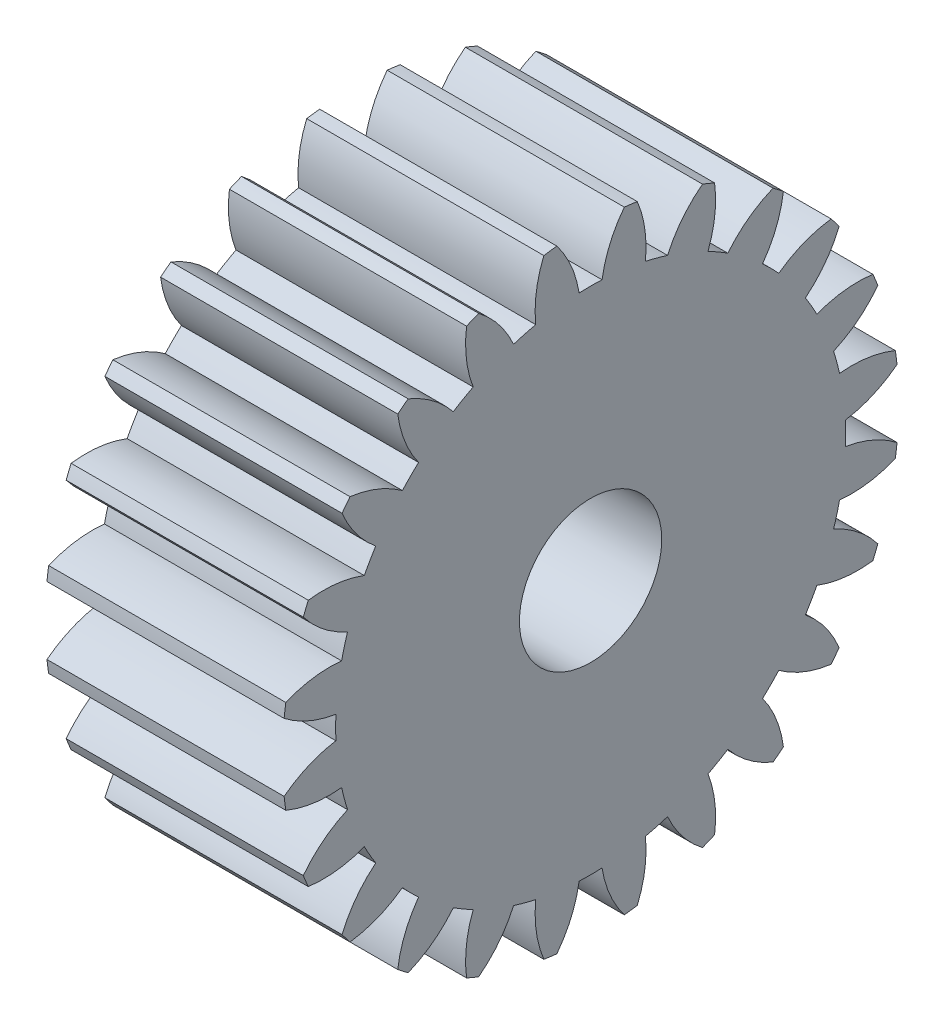
SolidWorks part; units mm, degrees
ref_plane "Plane1" through (0, 0, 0) normal (0, 0, 1) x (1, 0, 0)
ref_plane "Plane2" through (0, 0, 0) normal (0, 1, 0) x (1, 0, 0)
ref_plane "Plane3" through (0, 0, 0) normal (1, 0, 0) x (0, 0, -1)
other "Configuration Table"
sketch "HoldingSke" plane through (0, 0, 0) normal (0, 1, 0) x (1, 0, 0)
  line L0 (0, 0) -> (0.9135, -0.4067)
  line L1 (-15, 0) -> (100, 0) construction
  line L2 (0, 0) -> (-2.1039, 2.3779)
  line L3 (0, 0) -> (-11.863, 4.5341)
  line L4 (0, 0) -> (7.8894, 3.5126)
  line L5 (0, 0) -> (-46.8476, -17.4728)
  line L6 (0, 0) -> (-8.2896, -5.593)
  line L7 (-2.1039, 2.3779) -> (8.6586, 51.2059)
  line L8 (-76.2, 54.61) -> (-75.3, 54.61)
  line L9 (-71.009, 38.7566) -> (-53.1078, 45.2721)
  line L10 (-76.2, 71.12) -> (104.1128, 71.12)
  line L11 (0, 0) -> (-10, 0)
  line L12 (-76.2, 101.6) -> (-76.162, 101.6)
  line L13 (24.9733, 27.94) -> (52.9518, 28.4284)
  line L14 (24.9733, 27.94) -> (24.9743, 27.94)
  line L15 (24.9733, 27.94) -> (100.4006, 29.5858)
  line L16 (-63.627, -1) -> (-12.827, -1)
  circle A0 centre (0, 0) radius 2.5
  circle A1 centre (0, 0) radius 10.749
  circle A2 centre (0, 0) radius 37.5
  circle A3 centre (0, 0) radius 2.5
  dimension "MHD" = 21.498
  dimension "Hub_dia" = 75
  dimension "Bore" = 5
  dimension "MBD" = 5
  dimension "Num_teeth" = 24
  dimension "Pitch" = 1
  dimension "Overall_len" = 50
  dimension "Show_teeth" = 24
  dimension "Thickness" = 10
  dimension "OAL" = 50.0001
  dimension "T_dim" = 0.9
  dimension "Ap" = 20
  dimension "H" = 19.05
  dimension "Pitch_radius" = 180.3128
  dimension "Width" = 10
  dimension "Backlash" = 0.038
  dimension "Addendum_fac" = 1
  dimension "Dedendum_fac" = 1.25
  dimension "Clearance_fac" = 0.25
  dimension "Dedendum_add" = 0.001
  dimension "Module" = 1
sketch "BasProSke" plane through (0, 0, 0) normal (0, 1, 0) x (1, 0, 0)
  line L0 (-10, 0) -> (60, 0) construction
  line L1 (0, 0) -> (0, 13)
  line L2 (0, 0) -> (10, 0)
  line L3 (10, 0) -> (10, 13)
  line L4 (10, 13) -> (0, 13)
  dimension "Thickness" = 10
  dimension "Diameter" = 26
revolve "Base-Revolve" add sketch "BasProSke" angle 360 about L0
sketch "TooCutSke" plane through (0, 0, 0) normal (1, 0, 0) x (0, 0, -1)
  line L1 (0, 0) -> (0, 107) construction
  line L2 (0, 0) -> (-0.8513, 11.9698) construction
  line L3 (0, 0) -> (-3.127, 23.752) construction
  line L4 (-0.8513, 11.9698) -> (-1.5635, 11.876) construction
  arc A0 (0.4834, 10.7381) -> (-0.4834, 10.7381) centre (0, 0) ccw
  arc A1 (1.4409, 12.9455) -> (-1.4409, 12.9455) centre (0, 0) ccw
  circle A2 centre (0, 0) radius 12 construction
  circle A3 centre (0, 0) radius 11.2763 construction
  arc A4 (-0.4834, 10.7381) -> (-1.4409, 12.9455) centre (-5.2252, 9.9926) ccw
  arc A5 (1.4409, 12.9455) -> (0.4834, 10.7381) centre (5.2252, 9.9926) ccw
  dimension "Root_dia" = 21.498
  dimension "Overcut_dia" = 26.0508
  dimension "Pitch_dia" = 24
  dimension "Base_dia" = 22.5526
  dimension "Flank_rad" = 4.8
  dimension "Half_ang" = 7.5
  dimension "Half_CT" = 0.7183
extrude "ToothCut" cut sketch "TooCutSke" along normal through all
fillet "Breaks" [suppressed] radius 0.02
fillet "RootFillets" [suppressed] radius 0.251
pattern_circular "TeethCuts" count 24 every 15 about axis through (-10, 0, 0) along (1, 0, 0) of "ToothCut", "RootFillets", "Breaks"
sketch "HubNeaOneSke" plane through (0, 0, 0) normal (-1, 0, 0) x (0, 0, 1)
  circle A0 centre (0, 0) radius 10.749
  dimension "Diameter" = 21.498
extrude "HubNearOne" [suppressed] add sketch "HubNeaOneSke" along normal blind 40.0001
sketch "HubNeaBotSke" plane through (0, 0, 0) normal (-1, 0, 0) x (0, 0, 1)
  circle A0 centre (0, 0) radius 10.749
  dimension "Diameter" = 21.498
extrude "HubNearBoth" [suppressed] add sketch "HubNeaBotSke" along normal blind 20
ref_plane "FarPln" through (10, 0, 0) normal (1, 0, 0) x (0, 0, -1)
sketch "HubFarSke" plane through (10, 0, 0) normal (1, 0, 0) x (0, 0, -1)
  circle A0 centre (0, 0) radius 10.749
  dimension "Diameter" = 21.498
extrude "HubFar" [suppressed] add sketch "HubFarSke" along normal blind 20
sketch "BorSke" plane through (0, 0, 0) normal (1, 0, 0) x (0, 0, -1)
  circle A0 centre (0, 0) radius 2.5
  dimension "Diameter" = 5
extrude "Bore" cut sketch "BorSke" along normal mid plane 100.0001
sketch "KeySke" plane through (0, 0, 0) normal (1, 0, 0) x (0, 0, -1)
  line L0 (-1, 0) -> (-1, 3.4)
  line L1 (-1, 3.4) -> (1, 3.4)
  line L2 (1, 3.4) -> (1, 0)
  line L3 (0, 0) -> (0, 34) construction
  line L4 (-1, 0) -> (1, 0)
  dimension "Offset" = 3.4
  dimension "Width" = 2
extrude "Keyway" [suppressed] cut sketch "KeySke" along normal mid plane 100.0001
pattern_circular "Keyway2" [suppressed] count 2 every 90 about axis through (-10, 0, 0) along (1, 0, 0)
sketch "Sketch1" plane through (10, 0, 0) normal (1, 0, 0) x (0, 0, -1)
  circle A0 centre (0, 0) radius 3
  dimension "D1" = 6
extrude "Cut-Extrude1" cut sketch "Sketch1" against normal through all
equation "' \"Module@HoldingSke\" = 6.35"
equation "' \"Num_teeth@HoldingSke\" = 12"
equation "' \"Ap@HoldingSke\" =  20"
equation "' \"Ap@HoldingSke\" = 20"
equation "' \"Width@HoldingSke\" = 0.5 * 25.4"
equation "' \"Hub_dia@HoldingSke\"= 1 * 25.4"
equation "' \"Hub_dia@HoldingSke\" = 1 * 25.4"
equation "' \"Overall_len@HoldingSke\" = 1.0 * 25.4"
equation "' \"Bore@HoldingSke\" = 0.75 * 25.4"
equation "' \"T_dim@HoldingSke\" = 0.1 * 25.4"
equation "' \"Width@KeySke\" = 0.25 * 25.4"
equation "' \"Show_teeth@HoldingSke\" = 13"
equation "' \"Backlash@HoldingSke\" = 0.009 * 25.4"
equation "' \"Addendum_fac@HoldingSke\" = 1.0"
equation "' \"Dedendum_fac@HoldingSke\" = 1.25"
equation "' \"Dedendum_add@HoldingSke\" = 0.00005 * 25.4"
equation "' \"Clearance_fac@HoldingSke\" = 0.25"
equation "\"Pitch@HoldingSke\" = 1 / \"Module@HoldingSke\""
equation "\"Overcut_dia@TooCutSke\" = (\"Num_teeth@HoldingSke\" + 2 * \"Addendum_fac@HoldingSke\") / \"Pitch@HoldingSke\" + 0.002 * 25.4"
equation "\"Pitch_dia@TooCutSke\" = \"Num_teeth@HoldingSke\" / \"Pitch@HoldingSke\""
equation "\"Base_dia@TooCutSke\" = \"Num_teeth@HoldingSke\" / \"Pitch@HoldingSke\" * cos((\"Ap@HoldingSke\"  * 3.14159265 / 180))"
equation "\"Root_dia@TooCutSke\" = (\"Num_teeth@HoldingSke\" + 2) / \"Pitch@HoldingSke\" - 2 * (\"Addendum_fac@HoldingSke\" + \"Dedendum_fac@HoldingSke\") / \"Pitch@HoldingSke\" - \"Dedendum_add@HoldingSke\" * 2"
equation "\"Half_ang@TooCutSke\" = 180 / \"Num_teeth@HoldingSke\""
equation "\"Half_CT@TooCutSke\" = \"Num_teeth@HoldingSke\" / \"Pitch@HoldingSke\" * sin((3.14159265 / 2 / \"Num_teeth@HoldingSke\")) / 2 - 7 * \"Backlash@HoldingSke\" / 4"
equation "\"Flank_rad@TooCutSke\" = \"Num_teeth@HoldingSke\" / \"Pitch@HoldingSke\" / 5"
equation "\"Radius@RootFillets\" = \"Clearance_fac@HoldingSke\" / \"Pitch@HoldingSke\" + \"Dedendum_add@HoldingSke\""
equation "\"Break_rad@Breaks\" = 0.02 / \"Pitch@HoldingSke\""
equation "\"Thickness@HoldingSke\" = \"Width@HoldingSke\""
equation "\"OAL@HoldingSke\" = \"Thickness@HoldingSke\""
equation "\"MHD@HoldingSke\" = (\"Num_teeth@HoldingSke\" + 2) / \"Pitch@HoldingSke\" - 2 * (\"Addendum_fac@HoldingSke\" + \"Dedendum_fac@HoldingSke\")  / \"Pitch@HoldingSke\" - \"Dedendum_add@HoldingSke\" * 2"
equation "\"MBD@HoldingSke\" = (\"Num_teeth@HoldingSke\" + 2) / \"Pitch@HoldingSke\" - 2 * (\"Addendum_fac@HoldingSke\" + \"Dedendum_fac@HoldingSke\")  / \"Pitch@HoldingSke\" - \"Dedendum_add@HoldingSke\" * 2 - 0.002 * 25.4"
equation "\"MHD@HoldingSke\" = ((sgn( \"MHD@HoldingSke\" - \"Hub_dia@HoldingSke\" )-1)*( \"MHD@HoldingSke\" - \"Hub_dia@HoldingSke\" ))/-2+ \"Hub_dia@HoldingSke\""
equation "\"MBD@HoldingSke\" = ((sgn( \"MBD@HoldingSke\" - \"Bore@HoldingSke\" )-1)*( \"MBD@HoldingSke\" - \"Bore@HoldingSke\" ))/-2+ \"Bore@HoldingSke\""
equation "\"OAL@HoldingSke\" = ((sgn( \"OAL@HoldingSke\" - \"Overall_len@HoldingSke\" )+1)*( \"OAL@HoldingSke\" - \"Overall_len@HoldingSke\" ))/2 + \"Overall_len@HoldingSke\" + 0.000002 * 25.4"
equation "\"Num_teeth@TeethCuts\" = int( \"Show_teeth@HoldingSke\" ) + 1"
equation "\"Num_teeth@TeethCuts\" = ((sgn( \"Num_teeth@TeethCuts\" - \"Num_teeth@HoldingSke\" )-1)*( \"Num_teeth@TeethCuts\" - \"Num_teeth@HoldingSke\" ))/-2+ \"Num_teeth@HoldingSke\""
equation "\"Num_teeth@TeethCuts\" = ((sgn( \"Num_teeth@TeethCuts\" - 2.0)+1)*( \"Num_teeth@TeethCuts\" - 2.0))/2 +2.0"
equation "\"Angle@TeethCuts\" = 360.0 / \"Num_teeth@HoldingSke\""
equation "\"Diameter@BasProSke\" = (\"Num_teeth@HoldingSke\" + 2 * \"Addendum_fac@HoldingSke\") / \"Pitch@HoldingSke\""
equation "\"Thickness@BasProSke\"  = \"Thickness@HoldingSke\""
equation "' \"Fillet_rad@BasProSke\" =  \"Thickness@HoldingSke\" * 0.05"
equation "' \"Fillet_rad@BasProSke\" = \"Thickness@HoldingSke\" * 0.05"
equation "\"MHD@HoldingSke\" = ((sgn( \"MHD@HoldingSke\" - \"Root_dia@TooCutSke\" )-1)*( \"MHD@HoldingSke\" - \"Root_dia@TooCutSke\" ))/-2+ \"Root_dia@TooCutSke\""
equation "\"Diameter@HubNeaOneSke\" = \"MHD@HoldingSke\""
equation "\"Length@HubNearOne\" = \"OAL@HoldingSke\" - \"Thickness@BasProSke\""
equation "\"Diameter@HubNeaBotSke\" = \"MHD@HoldingSke\""
equation "\"Length@HubNearBoth\" = ( \"OAL@HoldingSke\" - \"Thickness@BasProSke\" ) / 2.0"
equation "\"Thickness@FarPln\" = \"Thickness@BasProSke\""
equation "\"Diameter@HubFarSke\" = \"MHD@HoldingSke\""
equation "\"Length@HubFar\" = ( \"OAL@HoldingSke\" - \"Thickness@BasProSke\" ) / 2.0"
equation "\"Diameter@BorSke\" = \"MBD@HoldingSke\""
equation "\"D1@Bore\" = \"OAL@HoldingSke\" * 2.0"
equation "\"D1@Keyway\" = \"OAL@HoldingSke\" * 2.0"
equation "\"Offset@KeySke\" = \"T_dim@HoldingSke\" + \"MBD@HoldingSke\" / 2.0"
